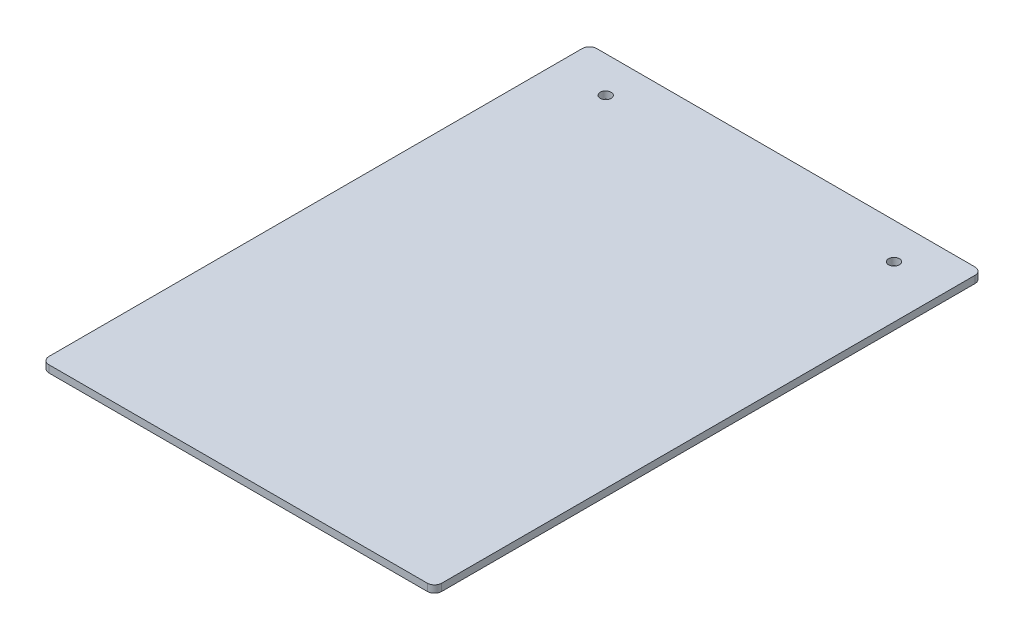
SolidWorks part; units mm, degrees
material "PC High Viscosity"
ref_plane "Front Plane" through (0, 0, 0) normal (0, 0, 1) x (1, 0, 0)
ref_plane "Top Plane" through (0, 0, 0) normal (0, 1, 0) x (1, 0, 0)
ref_plane "Right Plane" through (0, 0, 0) normal (1, 0, 0) x (0, 0, -1)
sketch "Sketch1" plane through (0, 0, 0) normal (0, 1, 0) x (1, 0, 0)
  line L1 (-173.0375, -241.3) -> (173.0375, -241.3)
  line L2 (-173.0375, -241.3) -> (-173.0375, 241.3)
  line L3 (-173.0375, 241.3) -> (173.0375, 241.3)
  line L4 (173.0375, -241.3) -> (173.0375, 241.3)
  line L5 (-173.0375, -241.3) -> (173.0375, 241.3) construction
  line L6 (-173.0375, 241.3) -> (173.0375, -241.3) construction
  point P0 (0, 0)
  dimension "D1" = 482.6
  dimension "D2" = 346.075
extrude "Boss-Extrude1" add sketch "Sketch1" along normal blind 6.35
fillet "Fillet1" radius 6.35 4 edges at (173.0375, 3.175, -241.3) (-173.0375, 3.175, -241.3) (-173.0375, 3.175, 241.3) (173.0375, 3.175, 241.3)
hole_wizard "3/8 (0.375) Diameter Hole1" positions "Sketch2" profile "Sketch3" hole size "3/8" standard "ANSI Inch" end condition through all
sketch "Sketch2" plane through (0, 6.35, 0) normal (0, 1, 0) x (1, 0, 0)
  line L0 (0, 241.3) -> (0, -241.3) construction
  line L1 (166.6875, 241.3) -> (-166.6875, 241.3) construction
  line L2 (-166.6875, -241.3) -> (166.6875, -241.3) construction
  point P0 (-127, 209.55)
  point P2 (127, 209.55)
  dimension "D1" = 31.75
  dimension "D2" = 127
sketch "Sketch3" plane through (-127, 6.35, -209.55) normal (1, 0, 0) x (0, 0, 1)
  line L0 (0, 0) -> (0, 6.35)
  line L1 (0, 6.35) -> (4.7625, 6.35)
  line L2 (4.7625, 6.35) -> (4.7625, 0)
  line L5 (4.7625, 0) -> (0, 0)
  line L11 (0, -6.35) -> (0, 107.95) construction
  dimension "Thru Hole Dia." = 9.525
  dimension "Thru Hole Depth" = 6.35
